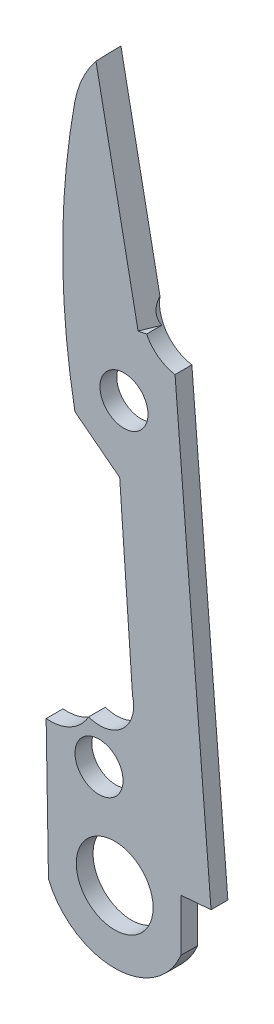
SolidWorks part; units mm, degrees
material "AISI 4340 Steel, normalized"
ref_plane "Front Plane" through (0, 0, 0) normal (0, 0, 1) x (1, 0, 0)
ref_plane "Top Plane" through (0, 0, 0) normal (0, 1, 0) x (1, 0, 0)
ref_plane "Right Plane" through (0, 0, 0) normal (1, 0, 0) x (0, 0, -1)
sketch "Sketch1" plane through (0, 0, 0) normal (0, 0, 1) x (1, 0, 0)
  line L0 (16.7881, 37.7732) -> (83.9405, 37.7732) construction
  line L1 (54.548, 56.6163) -> (56.6116, 46.195)
  line L2 (58.299, 43.8906) -> (60.2031, 20.3289)
  line L3 (60.2031, 20.3289) -> (58.6075, 20.2)
  line L4 (58.6075, 20.2) -> (58.6075, 17.4425)
  line L5 (51.4814, 24.727) -> (51.6051, 17.4425)
  line L6 (53.003, 39.5409) -> (55.3714, 37.7105)
  line L7 (55.3714, 37.7105) -> (56.0523, 28.0573)
  arc A0 (52.9934, 53.7093) -> (53.003, 39.5409) centre (91.6745, 46.6513) ccw
  arc A1 (52.9934, 53.7093) -> (54.548, 56.6163) centre (58.299, 52.7412) cw
  arc A2 (56.6116, 46.195) -> (58.299, 43.8906) centre (58.6075, 45.8865) ccw
  arc A3 (51.6051, 17.4425) -> (58.6075, 17.4425) centre (55.1063, 18.8908) ccw
  arc A4 (56.0523, 28.0573) -> (53.7245, 25.9246) centre (54.3184, 27.6131) cw
  arc A5 (53.7245, 25.9246) -> (51.4814, 24.727) centre (51.6858, 27.0436) cw
  circle A6 centre (55.5969, 41.3468) radius 1.27
  circle A7 centre (54.2776, 23.9125) radius 1.27
  dimension "D1" = 2.54
  dimension "D3" = 3.7889
  dimension "D7" = 5.3932
  dimension "D8" = 39.3197
  dimension "D12" = 2.3256
  dimension "D13" = 1.7899
  dimension "D2" = 8.6458
  dimension "D4" = 1.6008
  dimension "D5" = 36.625
  dimension "D6" = 0.585
  dimension "D9" = 2.9933
  dimension "D10" = 9.6531
  dimension "D11" = 7.2846
extrude "Boss-Extrude3" add sketch "Sketch1" along normal blind 0.889
sketch "Sketch3" plane through (0, 0, 0.889) normal (0, 0, 1) x (1, 0, 0)
  circle A0 centre (55.1063, 18.8908) radius 2.032
  dimension "D1" = 4.064
extrude "Cut-Extrude1" cut sketch "Sketch3" against normal through all
ref_plane "Plane2" through (-8.8976, 44.9328, 0) normal (-0.1942, 0.981, 0) x (0.981, 0.1942, 0)
sketch "Sketch4" plane through (-8.8976, 44.9328, 0) normal (-0.1942, 0.981, 0) x (0.981, 0.1942, 0)
  line L5 (64.5066, 0) -> (64.5066, -0.889)
  line L7 (62.4169, -0.889) -> (64.5066, -0.889) construction
  line L8 (63.9933, -0.889) -> (64.5066, -0.889)
  line L9 (63.9933, -0.889) -> (64.5066, 0)
  dimension "D1" = 30
extrude "Cut-Extrude2" cut sketch "Sketch4" against normal blind 12.7
